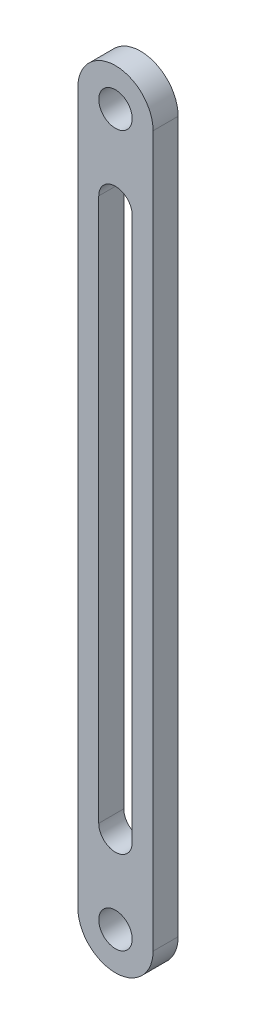
SolidWorks part; units mm, degrees
material "1023 Chapa de acero al carbono (SS)"
ref_plane "Alzado" through (0, 0, 0) normal (0, 0, 1) x (1, 0, 0)
ref_plane "Planta" through (0, 0, 0) normal (0, 1, 0) x (1, 0, 0)
ref_plane "Vista lateral" through (0, 0, 0) normal (1, 0, 0) x (0, 0, -1)
sketch "Croquis1" plane through (0, 0, 0) normal (0, 0, 1) x (1, 0, 0)
  line L0 (0, 0) -> (0, 10) construction
  line L1 (-4.5, 85) -> (-4.5, 0)
  line L2 (4.5, 0) -> (4.5, 85)
  line L3 (0, 85) -> (0, 75) construction
  line L4 (-2, 75) -> (-2, 10)
  line L5 (2, 10) -> (2, 75)
  circle A0 centre (0, 85) radius 2
  circle A1 centre (0, 0) radius 2
  arc A2 (4.5, 85) -> (-4.5, 85) centre (0, 85) ccw
  arc A3 (-4.5, 0) -> (4.5, 0) centre (0, 0) ccw
  arc A4 (2, 75) -> (-2, 75) centre (0, 75) ccw
  arc A5 (-2, 10) -> (2, 10) centre (0, 10) ccw
  dimension "D2" = 4
  dimension "D3" = 9
  dimension "D5" = 4
  dimension "D1" = 85
  dimension "D4" = 10
extrude "Saliente-Extruir1" add sketch "Croquis1" along normal blind 3
